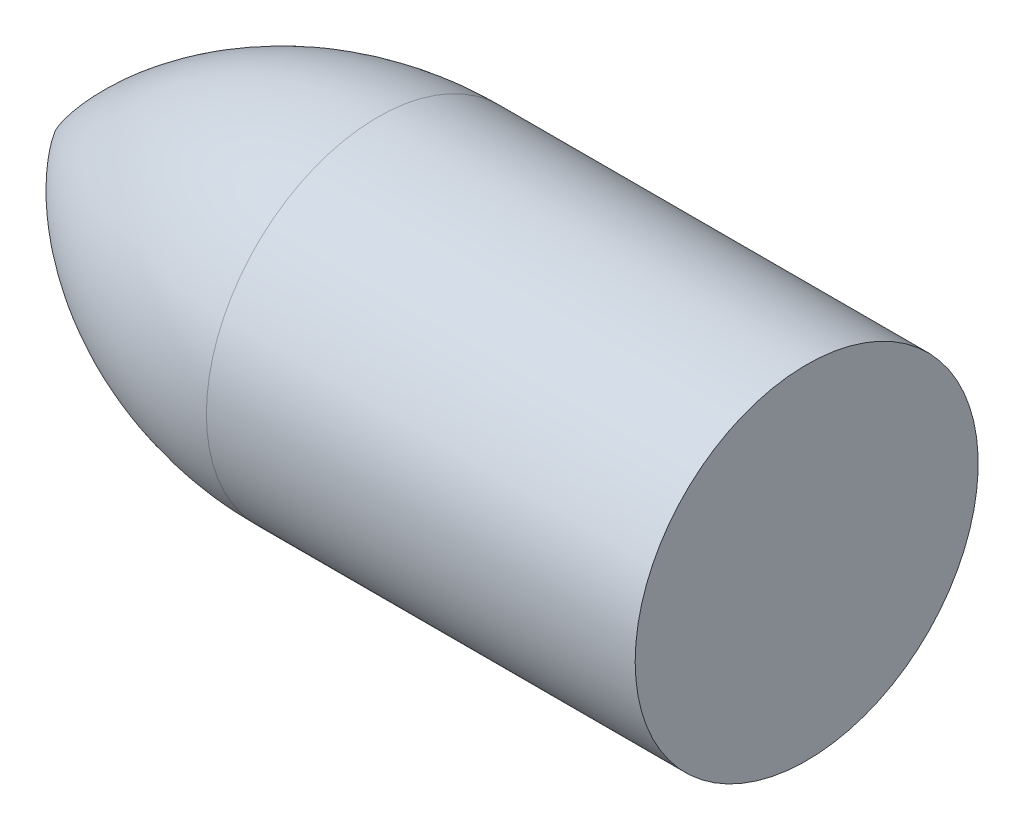
SolidWorks part; units mm, degrees
ref_plane "Front Plane" through (0, 0, 0) normal (0, 0, 1) x (1, 0, 0)
ref_plane "Top Plane" through (0, 0, 0) normal (0, 1, 0) x (1, 0, 0)
ref_plane "Right Plane" through (0, 0, 0) normal (1, 0, 0) x (0, 0, -1)
sketch "Sketch2" plane through (0, 0, 0) normal (0, 0, 1) x (1, 0, 0)
  line L0 (0, 0) -> (350, 0)
  line L1 (350, 0) -> (350, 80)
  line L2 (350, 80) -> (150, 80)
  arc A0 (150, 80) -> (0, 0) centre (150, -100.625) ccw
  dimension "D1" = 200
  dimension "D2" = 350
  dimension "D3" = 80
revolve "Revolve1" add sketch "Sketch2" angle 360 about L0
sketch3d "3DSketch1"
  line L0 (229.6045, 52.2196, 0) -> (122.1443, -85.2687, 0)
  line L1 (122.1443, -85.2687, 0) -> (144.0271, -102.3721, 0)
  line L2 (144.0271, -102.3721, 0) -> (253.9839, 38.3103, 0)
  line L3 (253.9839, 38.3103, 0) -> (229.6045, 52.2196, 0)
